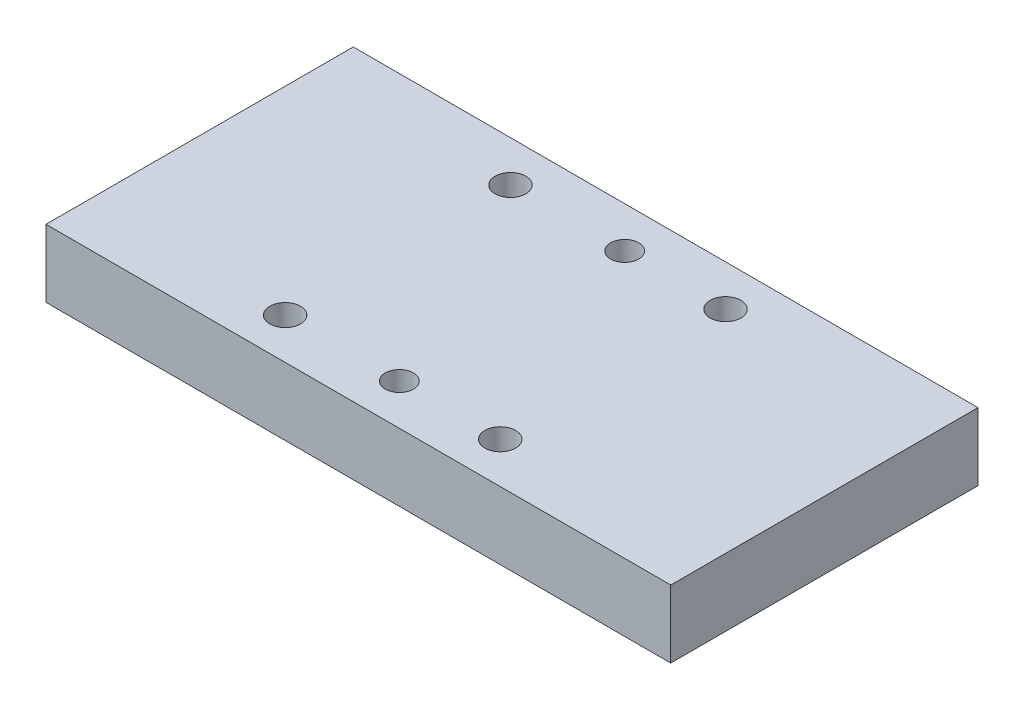
SolidWorks part; units mm, degrees
ref_plane "Front Plane" through (0, 0, 0) normal (0, 0, 1) x (1, 0, 0)
ref_plane "Top Plane" through (0, 0, 0) normal (0, 1, 0) x (1, 0, 0)
ref_plane "Right Plane" through (0, 0, 0) normal (1, 0, 0) x (0, 0, -1)
sketch "Sketch1" plane through (0, 0, 0) normal (0, 1, 0) x (1, 0, 0)
  line L0 (0, 0) -> (0, 5.7736) construction
  line L1 (61, -30) -> (-61, -30)
  line L2 (61, -30) -> (61, 30)
  line L3 (61, 30) -> (-61, 30)
  line L4 (-61, -30) -> (-61, 30)
  line L5 (61, -30) -> (-61, 30) construction
  line L6 (61, 30) -> (-61, -30) construction
  line L7 (0, 0) -> (0, 22) construction
  circle A0 centre (19.6981, 22) radius 3
  circle A1 centre (-22.3019, 22) radius 3
  circle A2 centre (-22.3019, -22) radius 3
  circle A3 centre (19.6981, -22) radius 3
  circle A4 centre (0, 22) radius 2.75
  circle A5 centre (0, -22) radius 2.75
  point P0 (0, 0)
  dimension "D3" = 6
  dimension "D4" = 6
  dimension "D5" = 6
  dimension "D6" = 6
  dimension "D11" = 5.5
  dimension "D12" = 5.5
  dimension "D1" = 122
  dimension "D2" = 60
  dimension "D7" = 42
  dimension "D8" = 42
  dimension "D9" = 44
  dimension "D10" = 22
extrude "Boss-Extrude2" add sketch "Sketch1" along normal blind 13.2
